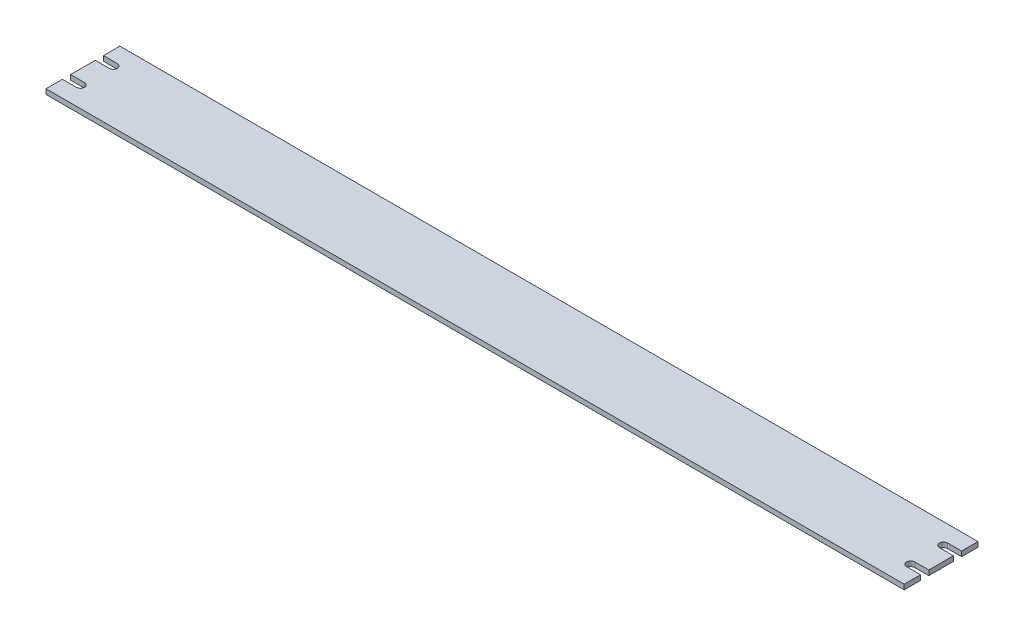
SolidWorks part; units mm, degrees
material "6061-T6 (SS)"
ref_plane "Front Plane" through (0, 0, 0) normal (0, 0, 1) x (1, 0, 0)
ref_plane "Top Plane" through (0, 0, 0) normal (0, 1, 0) x (1, 0, 0)
ref_plane "Right Plane" through (0, 0, 0) normal (1, 0, 0) x (0, 0, -1)
sketch "Sketch2" plane through (0, 0, 0) normal (0, 1, 0) x (1, 0, 0)
  line L1 (261.5, -22.5) -> (-261.5, -22.5)
  line L2 (261.5, -22.5) -> (261.5, 22.5)
  line L3 (261.5, 22.5) -> (-261.5, 22.5)
  line L4 (-261.5, -22.5) -> (-261.5, 22.5)
  line L5 (261.5, -22.5) -> (-261.5, 22.5) construction
  line L6 (261.5, 22.5) -> (-261.5, -22.5) construction
  point P0 (0, 0)
  dimension "D1" = 45
  dimension "D2" = 523
extrude "Boss-Extrude1" add sketch "Sketch2" along normal blind 3
sketch "Sketch3" plane through (0, 3, 0) normal (0, 1, 0) x (1, 0, 0)
  line L0 (-261.5, 10) -> (-253, 10) construction
  line L1 (-261.5, 22.5) -> (-261.5, -22.5) construction
  line L2 (-261.5, 12.5) -> (-253, 12.5)
  line L3 (-261.5, 7.5) -> (-253, 7.5)
  line L4 (-261.5, 0) -> (-271.296, 0) construction
  line L5 (-261.5, -10) -> (-253, -10) construction
  line L6 (-261.5, -12.5) -> (-253, -12.5)
  line L7 (-261.5, -7.5) -> (-253, -7.5)
  line L8 (0, 0) -> (0, 42.4581) construction
  line L9 (261.5, 10) -> (253, 10) construction
  line L10 (261.5, 12.5) -> (253, 12.5)
  line L11 (261.5, 7.5) -> (253, 7.5)
  line L12 (261.5, -10) -> (253, -10) construction
  line L13 (261.5, -12.5) -> (253, -12.5)
  line L14 (261.5, -7.5) -> (253, -7.5)
  arc A0 (-261.5, 12.5) -> (-261.5, 7.5) centre (-261.5, 10) ccw
  arc A1 (-253, 7.5) -> (-253, 12.5) centre (-253, 10) ccw
  arc A2 (-261.5, -12.5) -> (-261.5, -7.5) centre (-261.5, -10) cw
  arc A3 (-253, -7.5) -> (-253, -12.5) centre (-253, -10) cw
  arc A4 (261.5, 12.5) -> (261.5, 7.5) centre (261.5, 10) cw
  arc A5 (253, 7.5) -> (253, 12.5) centre (253, 10) cw
  arc A6 (261.5, -12.5) -> (261.5, -7.5) centre (261.5, -10) ccw
  arc A7 (253, -7.5) -> (253, -12.5) centre (253, -10) ccw
  point P4 (-257.25, 10)
  point P14 (-257.25, -10)
  point P23 (257.25, 10)
  point P30 (257.25, -10)
  dimension "D1" = 5
  dimension "D2" = 8.5
  dimension "D3" = 20
extrude "Cut-Extrude1" cut sketch "Sketch3" against normal through all
